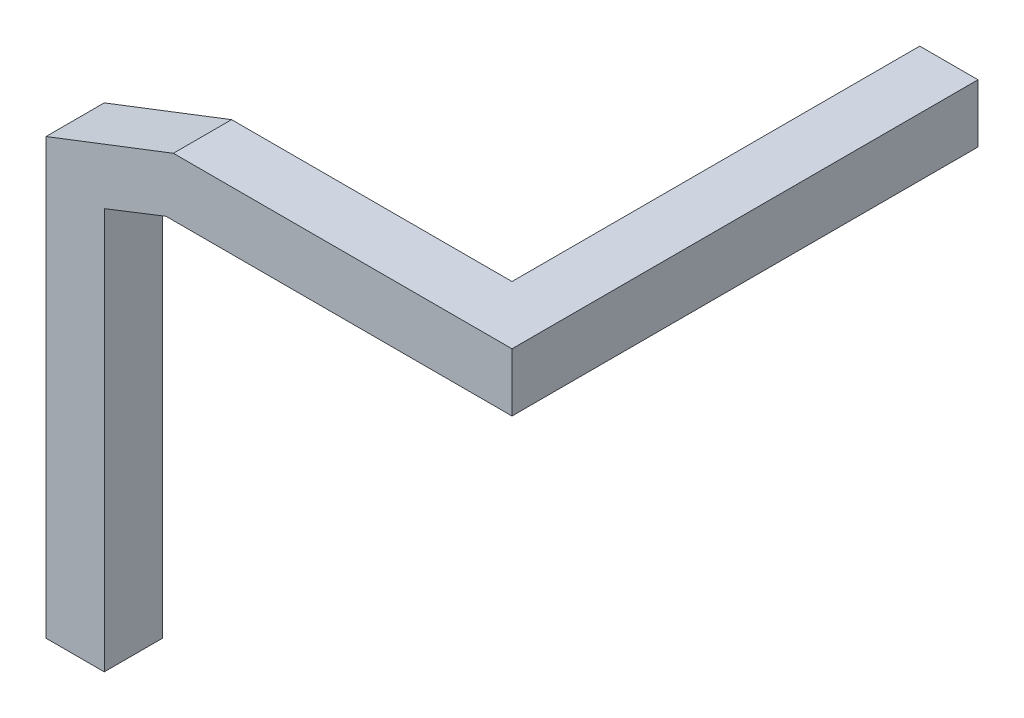
SolidWorks part; units mm, degrees
ref_plane "Front Plane" through (0, 0, 0) normal (0, 0, 1) x (1, 0, 0)
ref_plane "Top Plane" through (0, 0, 0) normal (0, 1, 0) x (1, 0, 0)
ref_plane "Right Plane" through (0, 0, 0) normal (1, 0, 0) x (0, 0, -1)
sketch "Sketch1" plane through (0, 0, 0) normal (0, 0, 1) x (1, 0, 0)
  line L0 (0, 0) -> (100, 0)
  line L1 (100, 0) -> (100, 100)
  line L2 (100, 100) -> (0, 100)
  line L3 (0, 100) -> (0, 0)
  dimension "D1" = 100
  dimension "D2" = 100
extrude "Boss-Extrude1" add sketch "Sketch1" along normal blind 800
sketch "Sketch2" plane through (0, 0, 0) normal (1, 0, 0) x (0, 0, -1)
  line L0 (-800, 100) -> (-700, 100)
  line L1 (-800, 100) -> (0, 100) construction
  line L2 (-700, 100) -> (-700, 0)
  line L3 (-800, 0) -> (0, 0) construction
  line L4 (-700, 0) -> (-800, 0)
  line L5 (-800, 0) -> (-800, 100)
  dimension "D1" = 100
extrude "Boss-Extrude2" add sketch "Sketch2" against normal blind 700
sketch "Sketch3" plane through (0, 0, 0) normal (0, 0, 1) x (1, 0, 0)
  line L0 (-481.3742, 100) -> (-700, 15.6312)
  line L1 (-700, 0) -> (-700, 100) construction
  line L2 (-1713.3699, -375.4331) -> (-481.3742, 100) construction
  line L3 (-700, 15.6312) -> (-700, 100)
  line L4 (-700, 100) -> (-481.3742, 100)
extrude "Cut-Extrude1" cut sketch "Sketch3" along normal through all
ref_plane "Plane1" through (0, 0, 800) normal (0, 0, 1) x (1, 0, 0)
sketch "Sketch4" plane through (0, 0, 800) normal (0, 0, 1) x (1, 0, 0)
  line L0 (-493.991, 0) -> (-600, -41.5645)
  line L1 (-700, 0) -> (100, 0) construction
  line L2 (-493.9453, 0.0179) -> (-1705.8453, -475.1496) construction
  line L7 (-700, 0) -> (-493.991, 0)
  line L8 (-700, -730.3561) -> (-600, -730.3561)
  line L9 (-600, -730.3561) -> (-600, -41.5645)
  line L10 (-700, 0) -> (-700, -730.3561)
extrude "Boss-Extrude3" add sketch "Sketch4" against normal blind 100 contours L7 L0 L9 L8 L10
ref_plane "Plane2" through (0, -730.3561, 0) normal (0, -1, 0) x (-1, 0, 0)
sketch "Sketch5" plane through (0, -730.3561, 0) normal (0, -1, 0) x (-1, 0, 0)
  line L0 (650, -700) -> (650, -800)
  line L1 (700, -700) -> (600, -700) construction
  line L2 (700, -800) -> (600, -800) construction
  circle A0 centre (650, -750) radius 25
extrude "Boss-Extrude4" add sketch "Sketch5" along normal blind 25 contours A0
